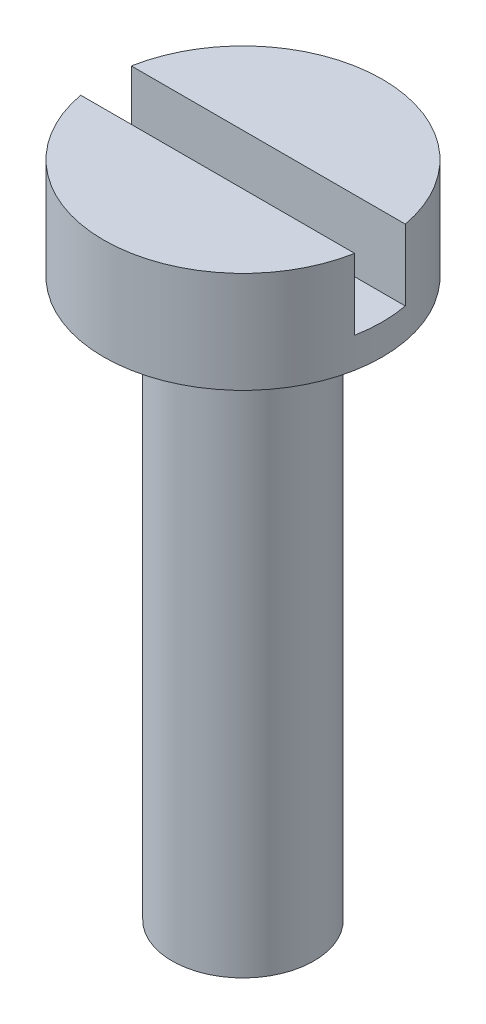
SolidWorks part; units mm, degrees
material "Nylon 6/10"
ref_plane "Front Plane" through (0, 0, 0) normal (0, 0, 1) x (1, 0, 0)
ref_plane "Top Plane" through (0, 0, 0) normal (0, 1, 0) x (1, 0, 0)
ref_plane "Right Plane" through (0, 0, 0) normal (1, 0, 0) x (0, 0, -1)
sketch "Sketch1" plane through (0, 0, 0) normal (0, 1, 0) x (1, 0, 0)
  circle A0 centre (0, 0) radius 2.75
  dimension "D1" = 5.5
extrude "Boss-Extrude1" add sketch "Sketch1" along normal blind 2
sketch "Sketch2" plane through (0, 0, 0) normal (0, -1, 0) x (1, 0, 0)
  circle A0 centre (0, 0) radius 1.4
  dimension "D1" = 2.8
extrude "Boss-Extrude2" add sketch "Sketch2" along normal blind 11
sketch "Sketch3" plane through (0, 0, 0) normal (1, 0, 0) x (0, 0, -1)
  line L0 (0, 1.1) -> (0, -1.1) construction
  line L1 (0.5, 2) -> (-0.5, 2)
  line L2 (0.5, 2) -> (0.5, 0.6)
  line L3 (0.5, 0.6) -> (-0.5, 0.6)
  line L4 (-0.5, 2) -> (-0.5, 0.6)
  line L5 (0.5, 2) -> (-0.5, 0.6) construction
  line L6 (0.5, 0.6) -> (-0.5, 2) construction
  line L7 (2.75, 2) -> (-2.75, 2) construction
  point P0 (0, 1.3)
  point P5 (0, 0)
  dimension "D1" = 1.4
  dimension "D2" = 1
extrude "Cut-Extrude1" cut sketch "Sketch3" against normal through all both and the other way through all
